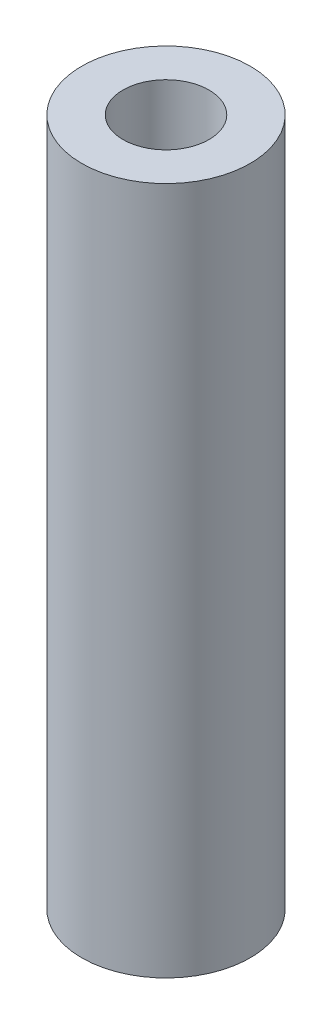
SolidWorks part; units mm, degrees
ref_plane "Front Plane" through (0, 0, 0) normal (0, 0, 1) x (1, 0, 0)
ref_plane "Top Plane" through (0, 0, 0) normal (0, 1, 0) x (1, 0, 0)
ref_plane "Right Plane" through (0, 0, 0) normal (1, 0, 0) x (0, 0, -1)
sketch "Sketch1" plane through (0, 0, 0) normal (0, 1, 0) x (1, 0, 0)
  circle A0 centre (0, 0) radius 3.1115
  circle A1 centre (0, 0) radius 1.5875
  dimension "D1" = 6.223
  dimension "D2" = 3.175
extrude "Boss-Extrude1" add sketch "Sketch1" along normal blind 25.4
